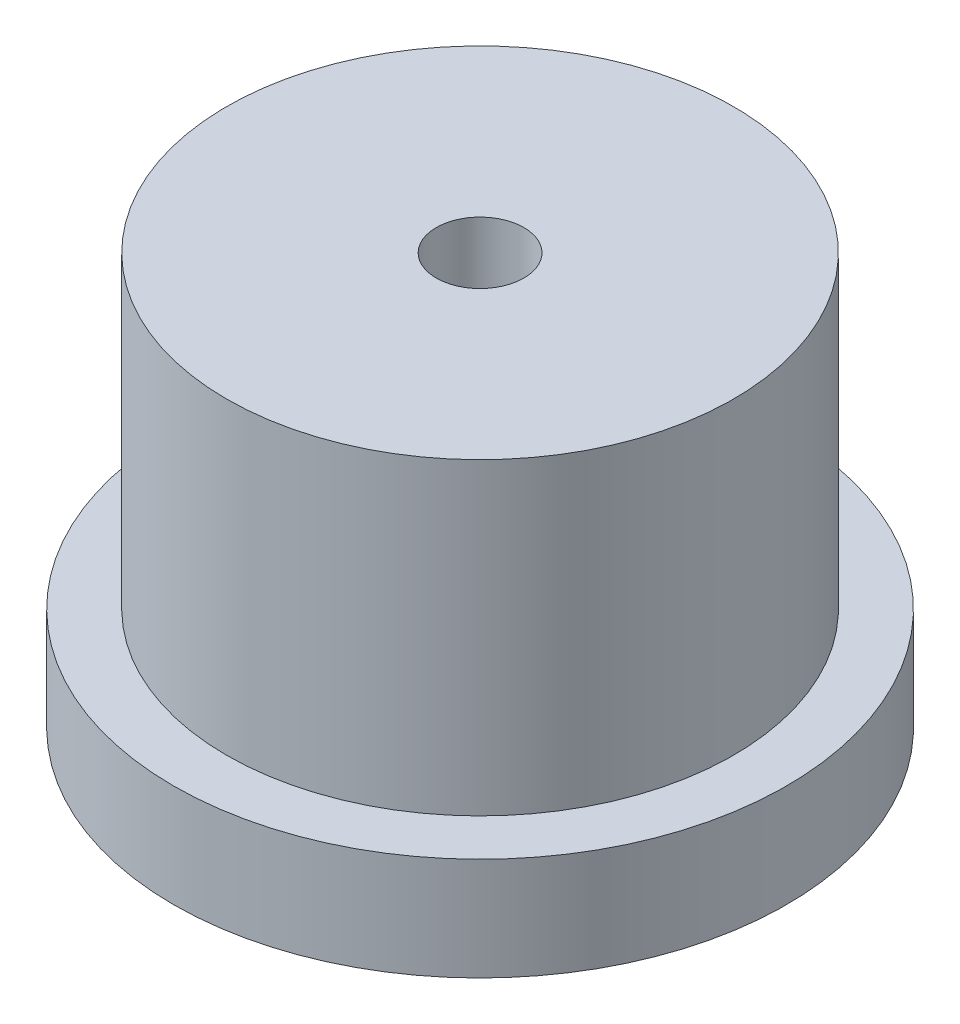
SolidWorks part; units mm, degrees
material "Stainless Steel"
ref_plane "Front Plane" through (0, 0, 0) normal (0, 0, 1) x (1, 0, 0)
ref_plane "Top Plane" through (0, 0, 0) normal (0, 1, 0) x (1, 0, 0)
ref_plane "Right Plane" through (0, 0, 0) normal (1, 0, 0) x (0, 0, -1)
sketch "Sketch1" plane through (0, 0, 0) normal (0, 1, 0) x (1, 0, 0)
  circle A0 centre (0, 0) radius 9.4615
  dimension "D1" = 18.923
extrude "Extrude1" add sketch "Sketch1" along normal blind 3.175
sketch "Sketch2" plane through (0, 3.175, 0) normal (0, 1, 0) x (1, 0, 0)
  circle A0 centre (0, 0) radius 7.8232
  dimension "D1" = 15.6464
extrude "Extrude2" add sketch "Sketch2" along normal blind 9.525
hole_wizard "#6-32 Tapped Hole2" positions "3DSketch4" profile "Sketch6" tap size "#6-32" standard "ANSI Inch" end condition through all
sketch3d "3DSketch4"
  point P0 (0, 0, 0)
sketch "Sketch6" plane through (0, 0, 0) normal (1, 0, 0) x (0, 0, -1)
  line L0 (0, 0) -> (0, 12.7)
  line L1 (0, 12.7) -> (1.3525, 12.7)
  line L2 (1.3525, 12.7) -> (1.3525, 0)
  line L5 (1.3525, 0) -> (0, 0)
  line L11 (0, -6.35) -> (0, 107.95) construction
  dimension "Thru Tap Drill Dia." = 2.7051
  dimension "Thru Tap Drill Depth" = 12.7
cosmetic thread "Hole Thread1" parameters "D2"=3.5052
